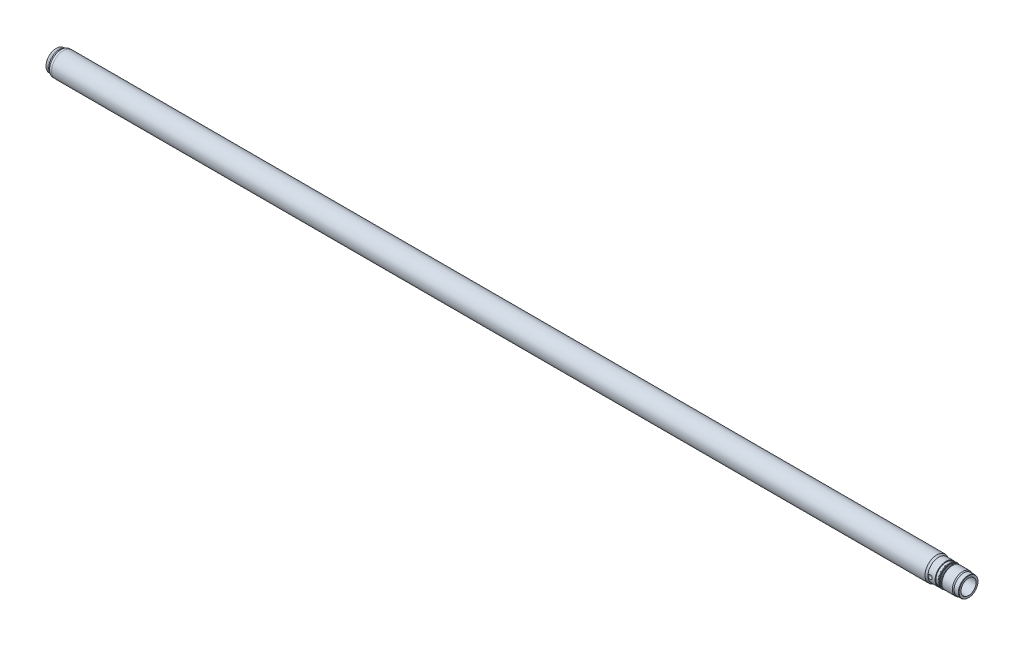
SolidWorks part; units mm, degrees
ref_plane "Front" through (0, 0, 0) normal (0, 0, 1) x (1, 0, 0)
ref_plane "Top" through (0, 0, 0) normal (0, 1, 0) x (1, 0, 0)
ref_plane "Right" through (0, 0, 0) normal (1, 0, 0) x (0, 0, -1)
sketch "Sketch1" plane through (0, 0, 0) normal (0, 0, 1) x (1, 0, 0)
  line L0 (0, 0) -> (2112, 0) construction
  line L1 (0, 21) -> (0, 23.5)
  line L2 (0.5, 24) -> (5, 24)
  line L3 (5, 24) -> (5, 24.75)
  line L4 (11.8301, 27.25) -> (17, 27.25)
  line L5 (17, 27.25) -> (17, 27.5)
  line L6 (5, 24.75) -> (7.5, 24.75)
  line L7 (7.5, 24.75) -> (11.8301, 27.25)
  line L8 (17, 27.5) -> (2038.6699, 27.5)
  line L9 (0, 21) -> (6.0622, 17.5)
  line L10 (6.0622, 17.5) -> (2112, 17.5)
  line L11 (2060, 24.5) -> (2060, 23.5)
  line L12 (2043, 25) -> (2059.5, 25)
  line L13 (2060, 23.5) -> (2066, 23.5)
  line L14 (2066, 23.5) -> (2066, 24.5)
  line L15 (2066.5, 25) -> (2068, 25)
  line L16 (2043, 25) -> (2038.6699, 27.5)
  line L17 (2068, 25) -> (2069, 24.4226)
  line L18 (2069, 24.4226) -> (2069, 23.75)
  line L19 (2070, 22.75) -> (2072, 22.75)
  line L20 (2072, 22.75) -> (2074.4533, 24)
  line L21 (2074.4533, 24) -> (2098.4019, 24)
  line L22 (2112, 21.9226) -> (2112, 17.5)
  line L23 (0.5, 24) -> (0, 23.5)
  line L24 (2098.4019, 24) -> (2101, 22.5)
  line L25 (2101, 22.5) -> (2111, 22.5)
  line L26 (2111, 22.5) -> (2112, 21.9226)
  arc A0 (2059.5, 25) -> (2060, 24.5) centre (2059.5, 24.5) cw
  arc A1 (2066, 24.5) -> (2066.5, 25) centre (2066.5, 24.5) cw
  arc A2 (2069, 23.75) -> (2070, 22.75) centre (2070, 23.75) ccw
  dimension "D35" = 0.5
  dimension "D36" = 1
  dimension "D3" = 5
  dimension "D4" = 48
  dimension "D5" = 1
  dimension "D6" = 46
  dimension "D7" = 30
  dimension "D8" = 7.5
  dimension "D9" = 35
  dimension "D10" = 30
  dimension "D11" = 42
  dimension "D12" = 48
  dimension "D13" = 45.5
  dimension "D14" = 27
  dimension "D15" = 69
  dimension "D16" = 30
  dimension "D17" = 6
  dimension "D18" = 43
  dimension "D19" = 3
  dimension "D20" = 47
  dimension "D21" = 2112
  dimension "D22" = 50
  dimension "D23" = 55
  dimension "D24" = 49.5
  dimension "D25" = 0.5
  dimension "D26" = 45
  dimension "D27" = 17
  dimension "D28" = 54.5
  dimension "D29" = 30
  dimension "D30" = 45
  dimension "D31" = 11
  dimension "D32" = 30
  dimension "D33" = 30
  dimension "D34" = 1
revolve "Base-Revolve" add sketch "Sketch1" angle 360 about L0
cosmetic thread "Cosmetic Thread1" parameters "D2"=45.835
sketch "Sketch2" plane through (0, 0, 0) normal (0, 0, 1) x (1, 0, 0)
  line L0 (0, 0) -> (2112, 0) construction
  line L4 (2112, -22.5) -> (2112, 22.5) construction
  circle A0 centre (2048, 0) radius 4.5
  dimension "D2" = 9
  dimension "D1" = 64
extrude "Cut-Extrude1" cut sketch "Sketch2" against normal mid plane 100
